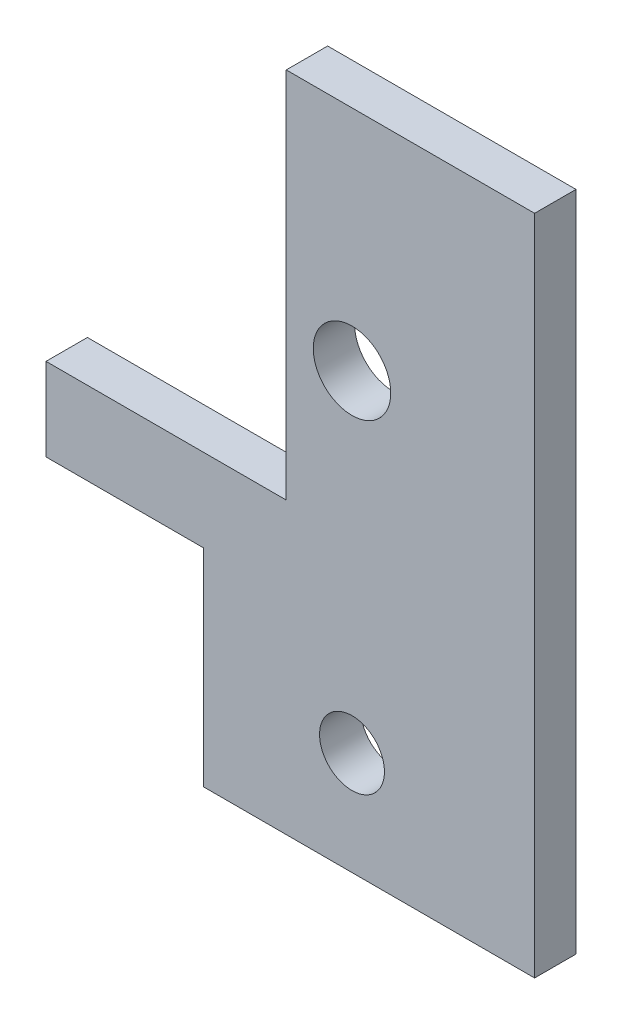
SolidWorks part; units mm, degrees
ref_plane "Front Plane" through (0, 0, 0) normal (0, 0, 1) x (1, 0, 0)
ref_plane "Top Plane" through (0, 0, 0) normal (0, 1, 0) x (1, 0, 0)
ref_plane "Right Plane" through (0, 0, 0) normal (1, 0, 0) x (0, 0, -1)
sketch "Sketch1" plane through (0, 0, 0) normal (0, 0, 1) x (1, 0, 0)
  line L0 (0, 9.5377) -> (0, -25.3873)
  line L5 (18.4277, -19.0373) -> (-28.7147, -19.0373)
  line L12 (-47.7647, -25.3873) -> (12.0777, -25.3873)
  line L13 (12.0777, -25.3873) -> (12.0777, -41.2623)
  line L14 (12.0777, -41.2623) -> (37.4777, -41.2623)
  line L15 (37.4777, -41.2623) -> (37.4777, 9.5377)
  line L16 (37.4777, 9.5377) -> (-47.7647, 9.5377)
  line L17 (-47.7647, 9.5377) -> (-47.7647, -25.3873)
  line L18 (18.4277, 3.1877) -> (18.4277, -19.0373)
  line L19 (18.4277, 3.1877) -> (-28.7147, 3.1877)
  circle A2 centre (23.4716, -33.3248) radius 2.4892
  circle A3 centre (23.4716, -7.9248) radius 2.9718
extrude "Boss-Extrude1" add sketch "Sketch1" along normal blind 3.175 contours L15 L16 L0 L12 L13 L14 A3 A2
sketch "Sketch2" plane through (0, 0, 0) normal (0, 0, -1) x (-1, 0, 0)
  line L0 (-37.4777, 9.5377) -> (0, 9.5377) construction
  line L1 (0, 3.1877) -> (-18.4277, 3.1877)
  line L2 (0, 3.1877) -> (0, 9.5377)
  line L3 (0, 9.5377) -> (-18.4277, 9.5377)
  line L4 (-18.4277, 3.1877) -> (-18.4277, 9.5377)
  line L5 (-18.4277, 3.1877) -> (-18.4277, -19.0373) construction
extrude "Cut-Extrude1" cut sketch "Sketch2" against normal through all
equation "\"Thick\"= \"in\""
